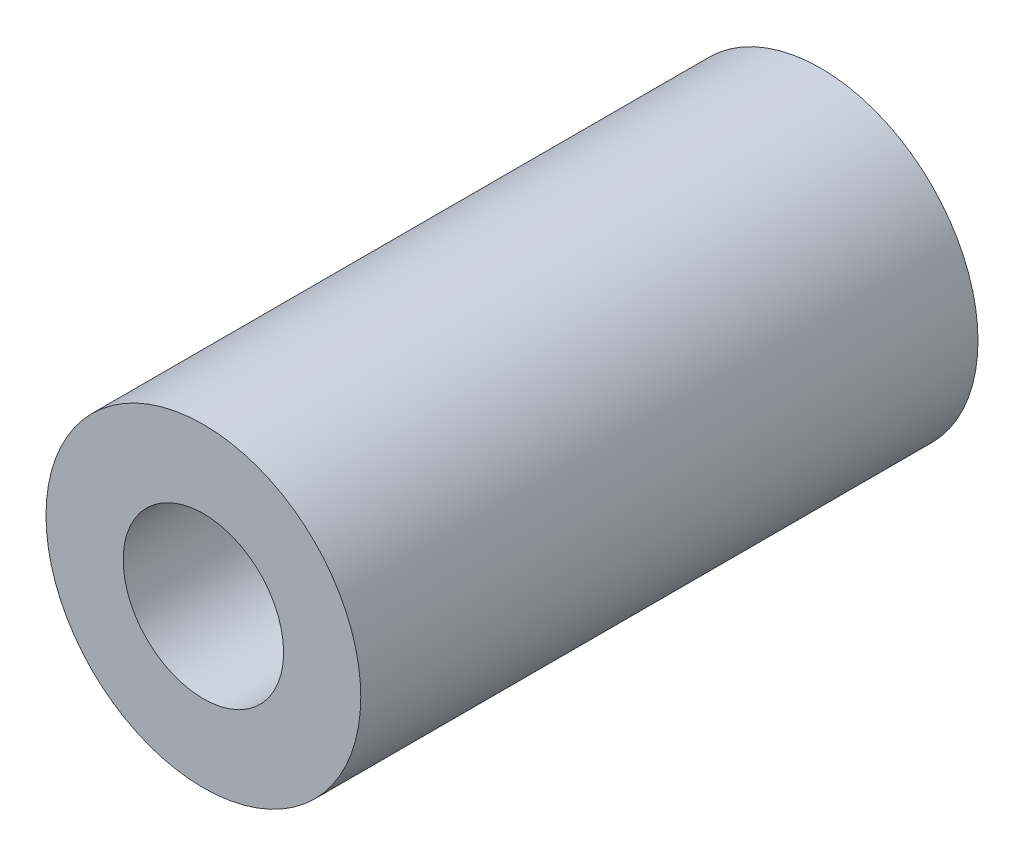
SolidWorks part; units mm, degrees
ref_plane "Alzado" through (0, 0, 0) normal (0, 0, 1) x (1, 0, 0)
ref_plane "Planta" through (0, 0, 0) normal (0, 1, 0) x (1, 0, 0)
ref_plane "Vista lateral" through (0, 0, 0) normal (1, 0, 0) x (0, 0, -1)
sketch "Croquis1" plane through (0, 0, 0) normal (0, 0, 1) x (1, 0, 0)
  circle A0 centre (0, 0) radius 2.6
  circle A1 centre (0, 0) radius 5.1
  dimension "D1" = 5.2
  dimension "D2" = 10.2
extrude "Saliente-Extruir1" add sketch "Croquis1" along normal blind 20
